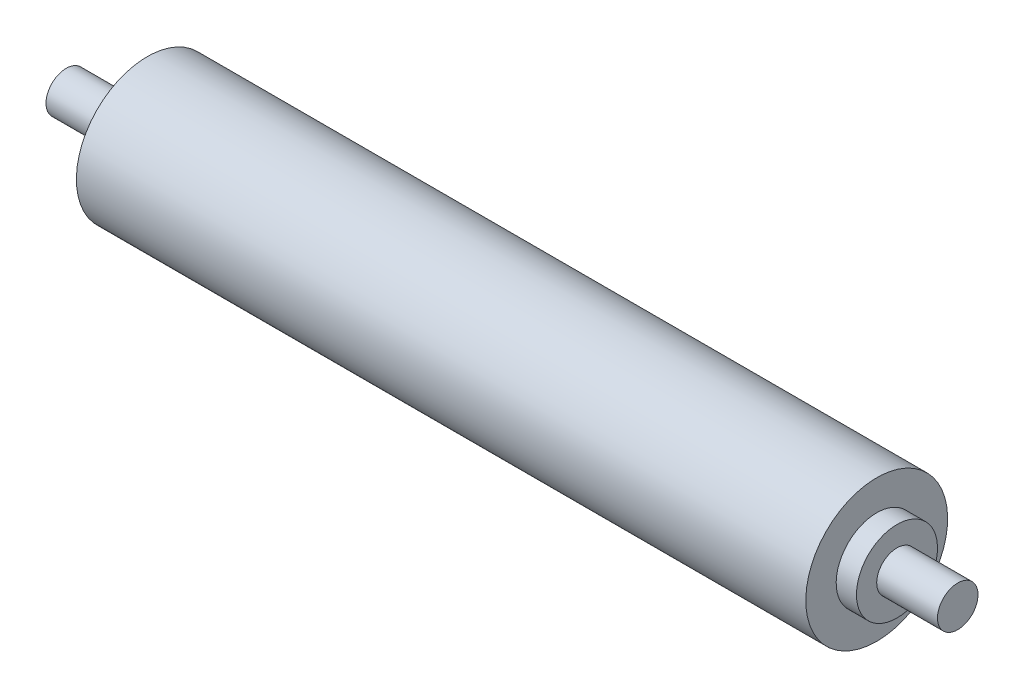
SolidWorks part; units mm, degrees
ref_plane "前视基准面" through (0, 0, 0) normal (0, 0, 1) x (1, 0, 0)
ref_plane "上视基准面" through (0, 0, 0) normal (0, 1, 0) x (1, 0, 0)
ref_plane "右视基准面" through (0, 0, 0) normal (1, 0, 0) x (0, 0, -1)
sketch "草图1" plane through (0, 0, 0) normal (0, 0, 1) x (1, 0, 0)
  line L0 (-230.7094, 0) -> (459.7941, 0) construction
  line L1 (0, 215.5466) -> (0, -189.8195) construction
  line L2 (-180, 35) -> (180, 35)
  line L6 (-220, 10) -> (-220, 0)
  line L7 (-190, 10) -> (-220, 10)
  line L8 (-180, 35) -> (-180, 20)
  line L9 (-220, 0) -> (220, 0)
  line L10 (-190, 10) -> (-190, 20)
  line L11 (-190, 20) -> (-180, 20)
  line L12 (220, 10) -> (220, 0)
  line L13 (190, 10) -> (220, 10)
  line L14 (190, 10) -> (190, 20)
  line L15 (190, 20) -> (180, 20)
  line L16 (180, 35) -> (180, 20)
  point P17 (0, 35)
  dimension "D1" = 20
  dimension "D2" = 10
  dimension "D3" = 35
  dimension "D4" = 360
  dimension "D5" = 30
  dimension "D6" = 380
  dimension "D7" = 440
revolve "旋转1" add sketch "草图1" angle 360 about L9
